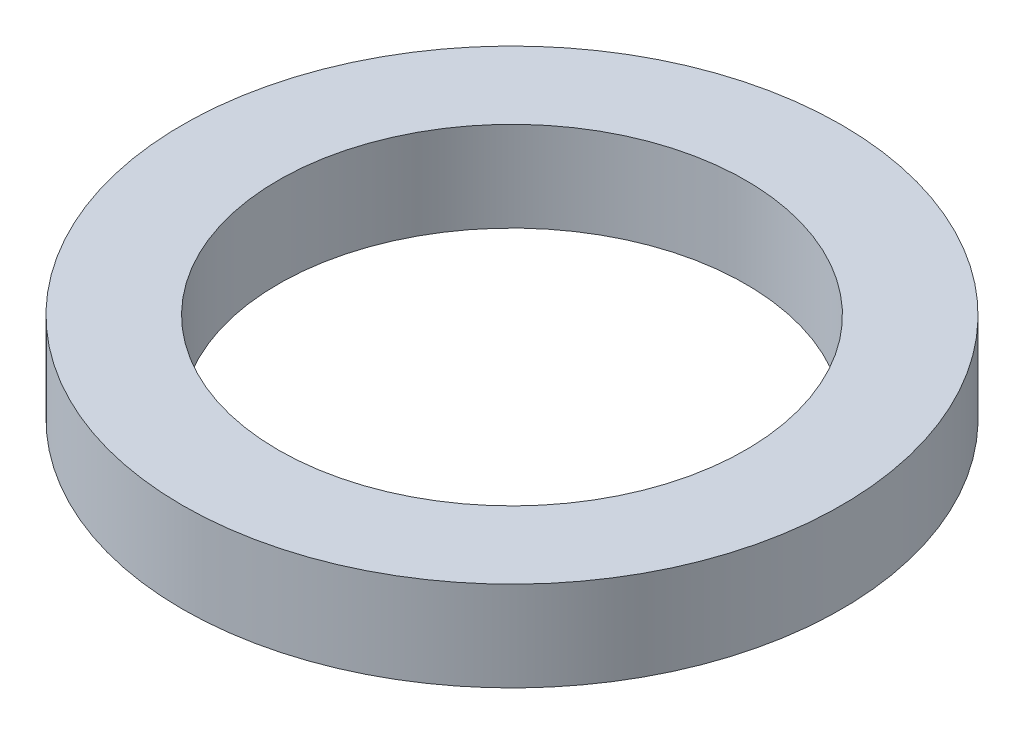
SolidWorks part; units mm, degrees
ref_plane "Front Plane" through (0, 0, 0) normal (0, 0, 1) x (1, 0, 0)
ref_plane "Top Plane" through (0, 0, 0) normal (0, 1, 0) x (1, 0, 0)
ref_plane "Right Plane" through (0, 0, 0) normal (1, 0, 0) x (0, 0, -1)
sketch "Sketch1" plane through (0, 0, 0) normal (0, 1, 0) x (1, 0, 0)
  circle A0 centre (0, 0) radius 9.906
  circle A1 centre (0, 0) radius 13.97
extrude "Boss-Extrude1" add sketch "Sketch1" along normal blind 3.81
